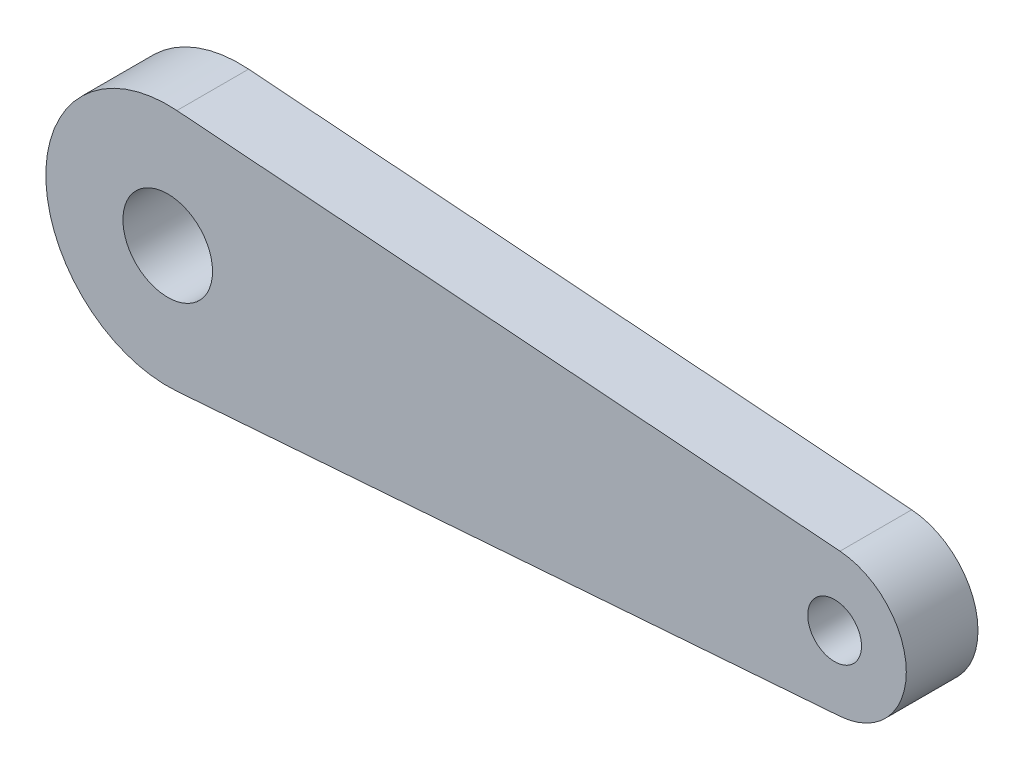
SolidWorks part; units mm, degrees
ref_plane "Front Plane" through (0, 0, 0) normal (0, 0, 1) x (1, 0, 0)
ref_plane "Top Plane" through (0, 0, 0) normal (0, 1, 0) x (1, 0, 0)
ref_plane "Right Plane" through (0, 0, 0) normal (1, 0, 0) x (0, 0, -1)
sketch "Sketch1" plane through (0, 0, 0) normal (0, 0, 1) x (1, 0, 0)
  line L0 (0.2559, 3.3904) -> (18.7505, 1.9943)
  line L1 (0.2559, -3.3904) -> (18.7505, -1.9943)
  arc A0 (0.2559, -3.3904) -> (0.2559, 3.3904) centre (0, 0) cw
  arc A1 (18.7505, 1.9943) -> (18.7505, -1.9943) centre (18.6, 0) cw
  circle A2 centre (18.6, 0) radius 0.75
  circle A3 centre (0, 0) radius 1.25
  point P8 (0, 0)
  point P10 (-0.1375, 0)
  dimension "D1" = 3.4
  dimension "D2" = 2
  dimension "D4" = 1.5
  dimension "D5" = 2.5
  dimension "D3" = 18.6
extrude "Main" add sketch "Sketch1" along normal blind 2
